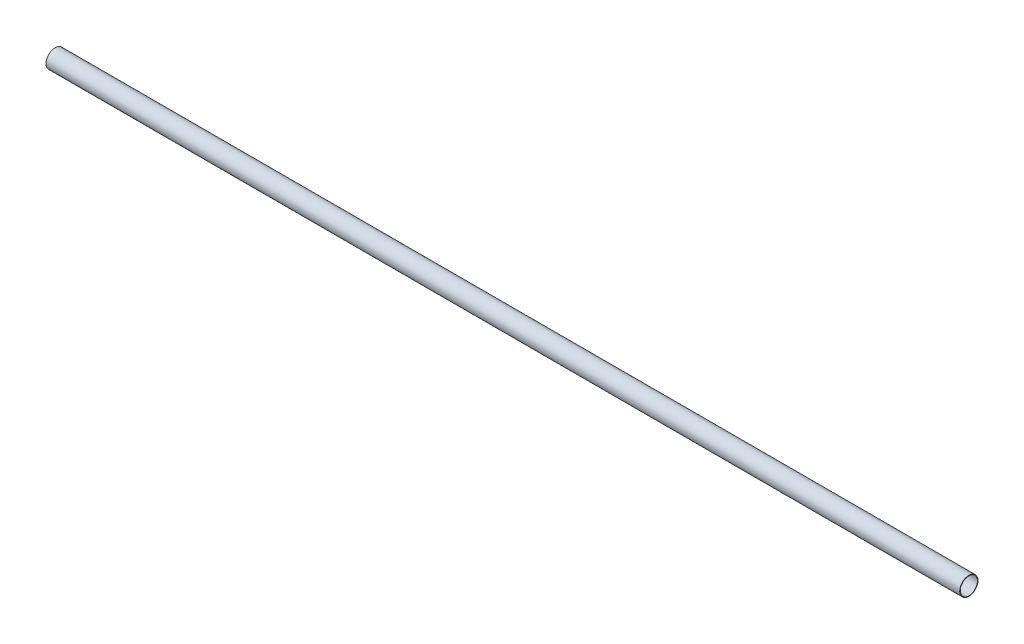
SolidWorks part; units mm, degrees
ref_plane "Front Plane" through (0, 0, 0) normal (0, 0, 1) x (1, 0, 0)
ref_plane "Top Plane" through (0, 0, 0) normal (0, 1, 0) x (1, 0, 0)
ref_plane "Right Plane" through (0, 0, 0) normal (1, 0, 0) x (0, 0, -1)
sketch "Sketch1" plane through (0, 0, 0) normal (1, 0, 0) x (0, 0, -1)
  circle A0 centre (0, 0) radius 25
  circle A1 centre (0, 0) radius 23.5
  dimension "D1" = 50
  dimension "D2" = 47
extrude "Boss-Extrude1" add sketch "Sketch1" along normal blind 2500
